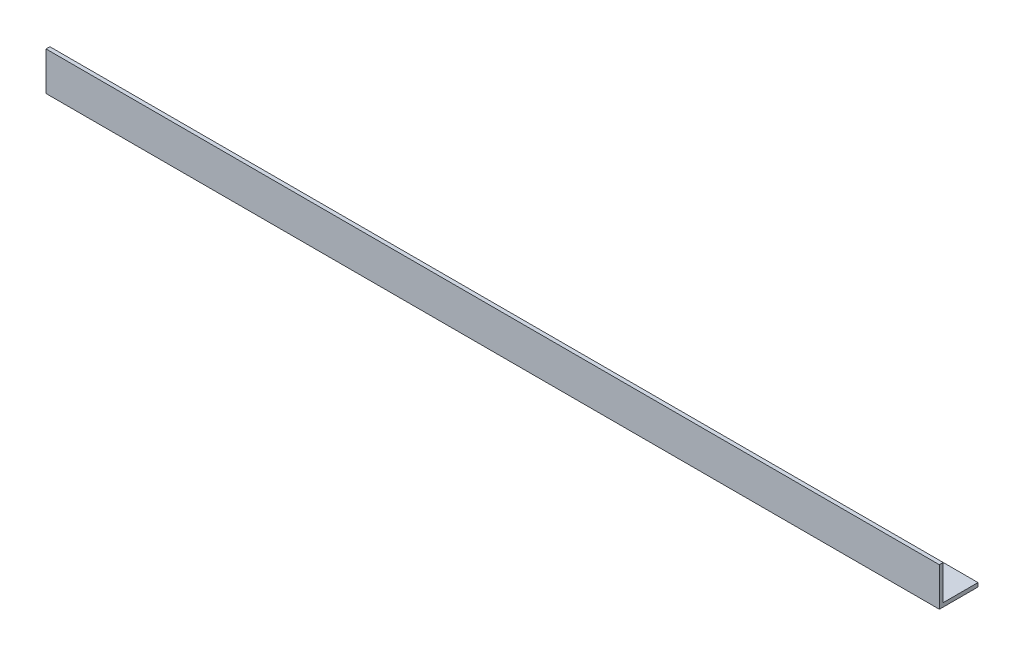
SolidWorks part; units mm, degrees
ref_plane "Спереди" through (0, 0, 0) normal (0, 0, 1) x (1, 0, 0)
ref_plane "Сверху" through (0, 0, 0) normal (0, 1, 0) x (1, 0, 0)
ref_plane "Справа" through (0, 0, 0) normal (1, 0, 0) x (0, 0, -1)
sketch "Эскиз1" plane through (0, 0, 0) normal (1, 0, 0) x (0, 0, -1)
  line L0 (0, 0) -> (0, 15)
  line L1 (0, 15) -> (1.5, 15)
  line L2 (1.5, 15) -> (1.5, 1.5)
  line L3 (1.5, 1.5) -> (15, 1.5)
  line L4 (15, 1.5) -> (15, 0)
  line L5 (15, 0) -> (0, 0)
  dimension "D1" = 15
  dimension "D2" = 15
  dimension "D3" = 1.5
  dimension "D4" = 1.5
extrude "Бобышка-Вытянуть1" add sketch "Эскиз1" along normal blind 347
